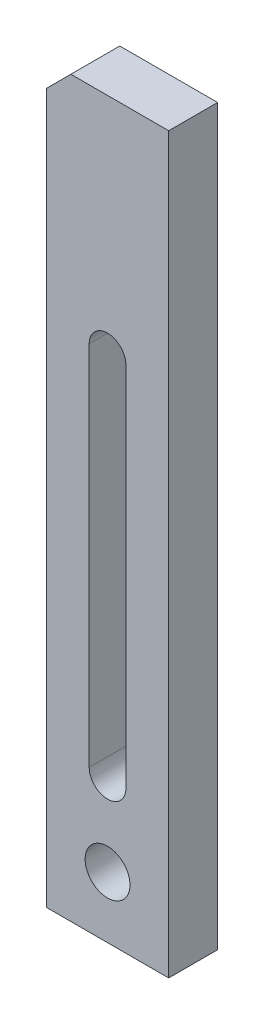
SolidWorks part; units mm, degrees
ref_plane "前视基准面" through (0, 0, 0) normal (0, 0, 1) x (1, 0, 0)
ref_plane "上视基准面" through (0, 0, 0) normal (0, 1, 0) x (1, 0, 0)
ref_plane "右视基准面" through (0, 0, 0) normal (1, 0, 0) x (0, 0, -1)
sketch "草图1" plane through (0, 0, 0) normal (0, 0, 1) x (1, 0, 0)
  line L1 (-15, 90) -> (15, 90)
  line L2 (-15, 90) -> (-15, -90)
  line L3 (-15, -90) -> (15, -90)
  line L4 (15, 90) -> (15, -90)
  line L5 (-15, 90) -> (15, -90) construction
  line L6 (-15, -90) -> (15, 90) construction
  point P0 (0, 0)
  dimension "D1" = 30
  dimension "D2" = 180
extrude "凸台-拉伸1" add sketch "草图1" along normal blind 12
sketch "草图2" plane through (0, 0, 12) normal (0, 0, 1) x (1, 0, 0)
  line L0 (0, 35) -> (0, -55) construction
  line L1 (4.5, 35) -> (4.5, -55)
  line L2 (-4.5, 35) -> (-4.5, -55)
  line L3 (-15, -90) -> (15, -90) construction
  line L4 (-15, 90) -> (-15, -90) construction
  arc A0 (4.5, 35) -> (-4.5, 35) centre (0, 35) ccw
  arc A1 (-4.5, -55) -> (4.5, -55) centre (0, -55) ccw
  circle A2 centre (0, -75) radius 5.5
  point P3 (0, -10)
  dimension "D4" = 11
  dimension "D1" = 9
  dimension "D2" = 90
  dimension "D3" = 20
  dimension "D5" = 15
  dimension "D6" = 15
extrude "切除-拉伸1" cut sketch "草图2" against normal blind 12
chamfer "倒角1" distance 6 angle 45 1 edges at (-15, 90, 6)
